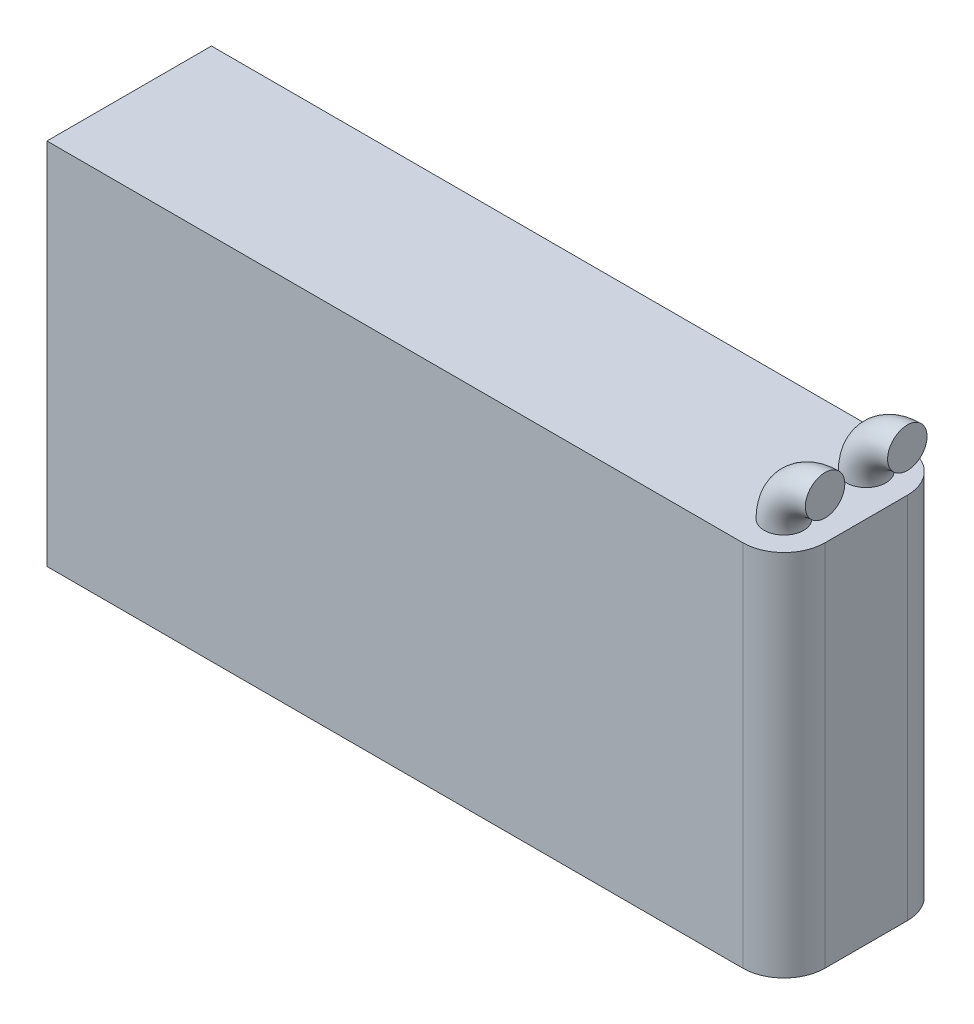
SolidWorks part; units mm, degrees
ref_plane "Front Plane" through (0, 0, 0) normal (0, 0, 1) x (1, 0, 0)
ref_plane "Top Plane" through (0, 0, 0) normal (0, 1, 0) x (1, 0, 0)
ref_plane "Right Plane" through (0, 0, 0) normal (1, 0, 0) x (0, 0, -1)
sketch "Sketch2" plane through (0, 0, 0) normal (0, 1, 0) x (1, 0, 0)
  line L1 (-35.56, 7.9375) -> (35.56, 7.9375)
  line L2 (-35.56, 7.9375) -> (-35.56, -7.9375)
  line L3 (-35.56, -7.9375) -> (35.56, -7.9375)
  line L4 (35.56, 7.9375) -> (35.56, -7.9375)
  line L5 (-35.56, 7.9375) -> (35.56, -7.9375) construction
  line L6 (-35.56, -7.9375) -> (35.56, 7.9375) construction
  point P0 (0, 0)
  dimension "D1" = 15.875
  dimension "D2" = 71.12
extrude "Boss-Extrude1" add sketch "Sketch2" along normal blind 35.56
fillet "Fillet1" radius 3.9688 2 edges at (35.56, 17.78, -7.9375) (35.56, 17.78, 7.9375)
sketch "Sketch3" plane through (0, 35.56, 0) normal (0, 1, 0) x (1, 0, 0)
  circle A0 centre (31.5913, -3.9688) radius 1.905
  circle A1 centre (31.5913, 3.9688) radius 1.905
  arc A2 (35.56, 3.9688) -> (31.5913, 7.9375) centre (31.5913, 3.9688) ccw construction
  arc A3 (31.5913, -7.9375) -> (35.56, -3.9688) centre (31.5913, -3.9688) ccw construction
  point P4 (0, 0)
  dimension "D1" = 3.81
revolve "Revolve1" add sketch "Sketch3" angle 90 about axis through (35.56, 35.56, -7.9375) along (0, 0, -1)
equation "\"AIRFRAME_OD\"= 3.142in"
equation "\"AIRFRAME_ID\"= 3.00in"
equation "\"FLAT_T\"= 0.125in"
equation "\"NOSE_EXP_L\"= 3.5in"
equation "\"NOSE_SHOULDER_L\"= 1.5in"
equation "\"MAIN_L\"= 30in"
equation "\"RECO_COUP_L\"= 6in"
equation "\"RECO_SWITCH_L\"= 1.5in"
equation "\"DROGUE_L\"= 14in"
equation "\"ATS_FORE_COUP_L\"= 4in"
equation "\"ATS_AFT_COUP_L\"= 2.5in"
equation "\"LOWER_L\"= 16in"
equation "\"FIN_N\"= 4"
equation "\"CR_AFT_X\"= 0.5in"
equation "\"CR_FORE_X\"= 6in"
equation "\"COUPLER_OD\"= 2.998in"
equation "\"COUPLER_ID\"= 2.875in"
equation "\"RECO_ROD_X\"= 1.5in"
equation "\"ATS_ROD_X\"= 2in"
equation "\"FIN_ROOT\"= 5in"
equation "\"FIN_X\"= 0.75in"
equation "\"MOTOR_OD\"= 2.25in"
equation "\"MOTOR_ID\"= 2.126in"
equation "\"MOTOR_L\"= 8in"
equation "\"MOTOR_LOWER_X\"= 0.5in"
equation "\"NOSE_CONE_L\"=14.5in"
equation "\"ATS_LIPO_L\" = 2.8in"
equation "\"ATS_LIPO_W\" = 0.625in"
equation "\"ATS_LIPO_H\" = 1.4in "
equation "\"ATS_STANDOFF_H\" = 10mm"
equation "\"ATS_STANDOFF_OD\" = 5.2mm"
equation "\"ATS_PCB_L\" = 2.5in"
equation "\"ATS_PCB_W\" = 1.45in"
equation "\"ATS_PCB_H\" = 1.2in"
equation "\"ATS_PCB_HOLESEP_W\" = 1.33in - 0.0985in"
equation "\"ATS_ALTI_L\" = 1.05in"
equation "\"ATS_ALTI_W\" = 0.7in"
equation "\"ATS_ALTI_H\" = 0.4in"
equation "\"D1@Sketch2\"=\"ATS_LIPO_W\""
equation "\"D2@Sketch2\"=\"ATS_LIPO_L\""
equation "\"D1@Boss-Extrude1\"=\"ATS_LIPO_H\""
equation "\"D1@Fillet1\"=\"ATS_LIPO_W\"/4"
